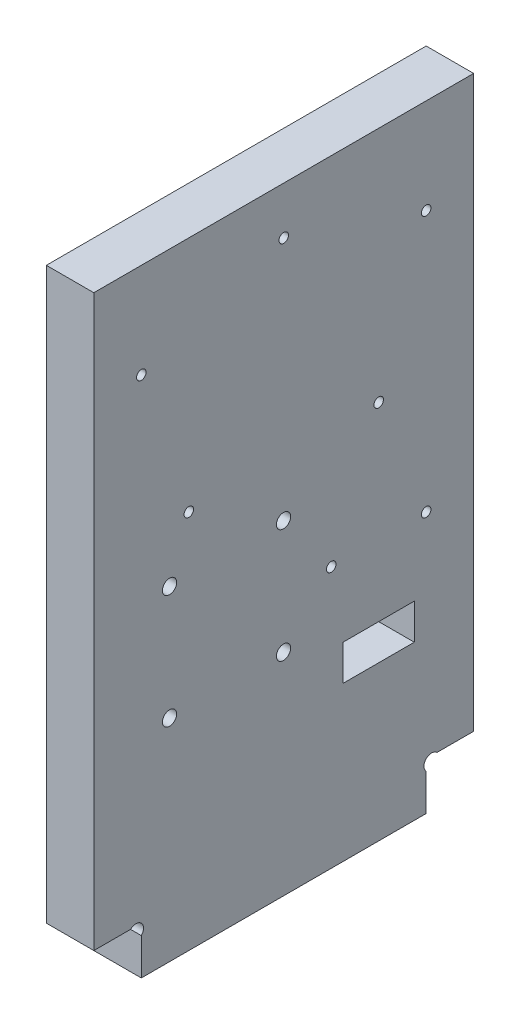
SolidWorks part; units mm, degrees
ref_plane "Plan de face" through (0, 0, 0) normal (0, 0, 1) x (1, 0, 0)
ref_plane "Plan de dessus" through (0, 0, 0) normal (0, 1, 0) x (1, 0, 0)
ref_plane "Plan de droite" through (0, 0, 0) normal (1, 0, 0) x (0, 0, -1)
sketch "Esquisse1" plane through (0, 0, 0) normal (1, 0, 0) x (0, 0, -1)
  line L8 (10, 7.7373) -> (10, 0)
  line L9 (70, 7.7373) -> (70, 0)
  line L10 (7.7373, 10) -> (0, 10)
  line L11 (10, 0) -> (70, 0)
  line L12 (72.2627, 10) -> (80, 10)
  line L13 (0, 10) -> (0, 130)
  line L14 (0, 130) -> (80, 130)
  line L15 (80, 130) -> (80, 10)
  arc A0 (10, 7.7373) -> (7.7373, 10) centre (8.8686, 8.8686) ccw
  arc A1 (70, 7.7373) -> (72.2627, 10) centre (71.1314, 8.8686) cw
  dimension "D7" = 1.1314
  dimension "D6" = 1.6
  dimension "D1" = 10
  dimension "D2" = 10
  dimension "D3" = 10
  dimension "D4" = 80
  dimension "D5" = 130
  dimension "D8" = 1.1314
  dimension "D9" = 1.1314
  dimension "D10" = 1.1314
extrude "Extrusion1" add sketch "Esquisse1" along normal blind 10
sketch "Esquisse2" plane through (10, 0, 0) normal (1, 0, 0) x (0, 0, -1)
  line L0 (0, 10) -> (7.7373, 10) construction
  line L1 (0, 130) -> (0, 10) construction
  line L2 (80, 10) -> (80, 130) construction
  line L3 (72.2627, 10) -> (80, 10) construction
  line L4 (80, 130) -> (0, 130) construction
  circle A0 centre (60, 80) radius 1
  circle A1 centre (10, 110) radius 1
  circle A2 centre (20, 80) radius 1
  circle A3 centre (70, 110) radius 1
  circle A4 centre (15.95, 68.45) radius 1.5
  circle A5 centre (15.95, 44.45) radius 1.5
  circle A6 centre (39.95, 44.45) radius 1.5
  circle A7 centre (39.95, 68.45) radius 1.5
  circle A8 centre (40, 120) radius 1
  circle A9 centre (70, 55) radius 1
  circle A10 centre (50, 55) radius 1
  dimension "D5" = 15.95
  dimension "D7" = 10
  dimension "D9" = 10
  dimension "D4" = 3
  dimension "D6" = 2
  dimension "D1" = 58.45
  dimension "D2" = 24
  dimension "D3" = 24
  dimension "D8" = 40
  dimension "D10" = 30
  dimension "D11" = 10
  dimension "D12" = 20
  dimension "D13" = 10
  dimension "D14" = 10
  dimension "D15" = 10
  dimension "D16" = 20
  dimension "D17" = 45
extrude "Enlèv. mat.-Extru.1" cut sketch "Esquisse2" against normal through all
sketch "Esquisse3" plane through (0, 0, 0) normal (-1, 0, 0) x (0, 0, 1)
  line L1 (-67.5, 40) -> (-52.5, 40)
  line L2 (-67.5, 40) -> (-67.5, 32.5)
  line L3 (-67.5, 32.5) -> (-52.5, 32.5)
  line L4 (-52.5, 40) -> (-52.5, 32.5)
  circle A0 centre (-70, 55) radius 1 construction
  circle A1 centre (-50, 55) radius 1 construction
  dimension "D4" = 2.5
  dimension "D1" = 15
  dimension "D2" = 7.5
  dimension "D3" = 15
  dimension "D5" = 2.5
extrude "Enlèv. mat.-Extru.2" cut sketch "Esquisse3" against normal through all
